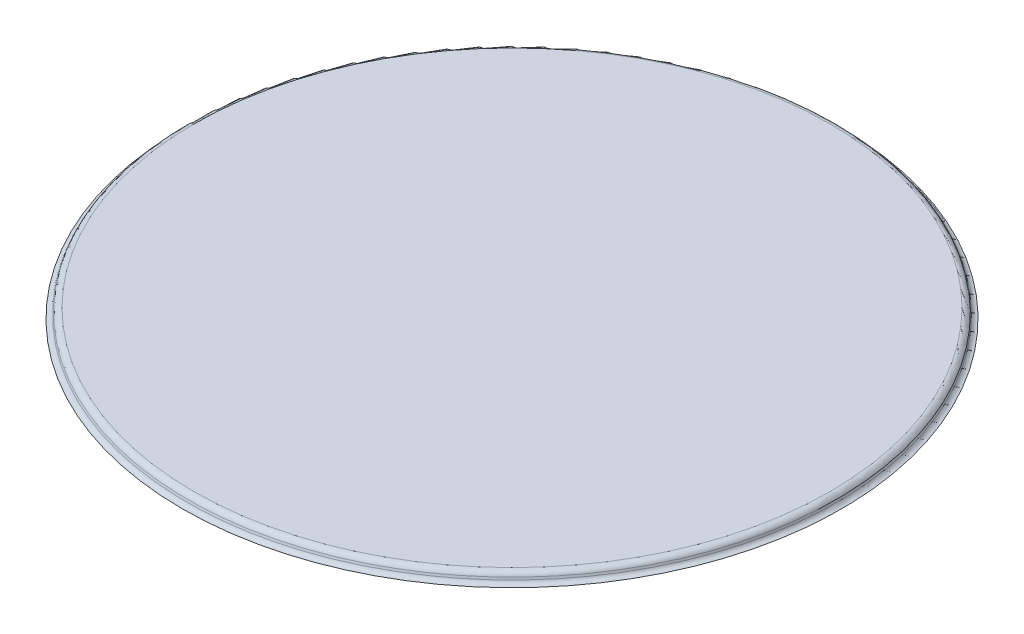
SolidWorks part; units mm, degrees
ref_plane "Ebene vorne" through (0, 0, 0) normal (0, 0, 1) x (1, 0, 0)
ref_plane "Ebene oben" through (0, 0, 0) normal (0, 1, 0) x (1, 0, 0)
ref_plane "Ebene rechts" through (0, 0, 0) normal (1, 0, 0) x (0, 0, -1)
sketch "Skizze1" plane through (0, 0, 0) normal (0, 1, 0) x (1, 0, 0)
  circle A0 centre (0, 0) radius 75
  dimension "D1" = 150
extrude "Aufsatz-Linear austragen1" add sketch "Skizze1" along normal blind 10
sketch "Skizze7" plane through (0, 0, 0) normal (0, 0, 1) x (1, 0, 0)
  line L0 (0, 0) -> (0, 48.0834) construction
  line L1 (-52.5, 0) -> (-52.5, 46.0723) construction
  line L2 (-75, 0) -> (75, 0) construction
  line L3 (-51.7482, 10.5264) -> (-51.6334, 10.842)
  line L4 (75, 10) -> (-75, 10) construction
  line L5 (-50.6937, 11.5) -> (0, 11.5)
  line L6 (0, 11.5) -> (0, 10)
  line L7 (0, 10) -> (-52.5, 10)
  arc A0 (-51.6334, 10.842) -> (-50.6937, 11.5) centre (-50.6937, 10.5) cw
  arc A1 (-51.7482, 10.5264) -> (-52.5, 10) centre (-52.5, 10.8) cw
  dimension "D2" = 0.8
  dimension "D3" = 1
  dimension "D1" = 52.5
  dimension "D4" = 1.5
  dimension "D5" = 20
revolve "Rotation1" add sketch "Skizze7" angle 360 about L0
sketch "Skizze8" plane through (0, 0, 0) normal (0, -1, 0) x (1, 0, 0)
  circle A1 centre (0, 0) radius 75
  circle A2 centre (0, 0) radius 75
  dimension "D1" = 0
extrude "Schnitt-Linear austragen1" cut sketch "Skizze8" against normal up to surface (10 mm away) up to face at (0, 10, -52.5)
sketch "Ausrichtungsskizze" plane through (0, 10, 0) normal (0, -1, 0) x (-1, 0, 0)
  circle A0 centre (0, 0) radius 52.5 construction
  circle A1 centre (0, 0) radius 52.5
  point P3 (0, 0)
other "Formwerkzeug1"
